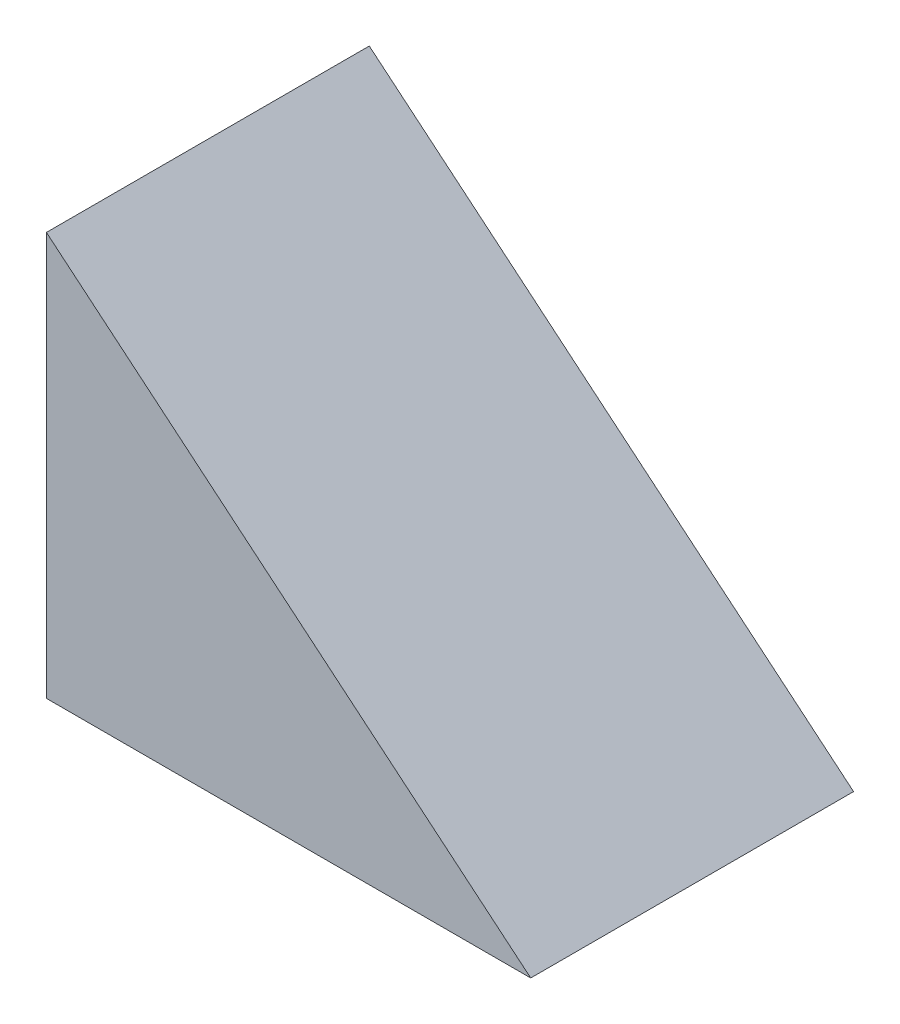
SolidWorks part; units mm, degrees
ref_plane "Front" through (0, 0, 0) normal (0, 0, 1) x (1, 0, 0)
ref_plane "Top" through (0, 0, 0) normal (0, 1, 0) x (1, 0, 0)
ref_plane "Right" through (0, 0, 0) normal (1, 0, 0) x (0, 0, -1)
sketch "Sketch1" plane through (0, 0, 0) normal (0, 0, 1) x (1, 0, 0)
  line L0 (0, 0) -> (0, 25)
  line L1 (0, 25) -> (30, 0)
  line L2 (30, 0) -> (0, 0)
  dimension "D1" = 25
  dimension "D2" = 30
extrude "Boss-Extrude1" add sketch "Sketch1" along normal blind 20
